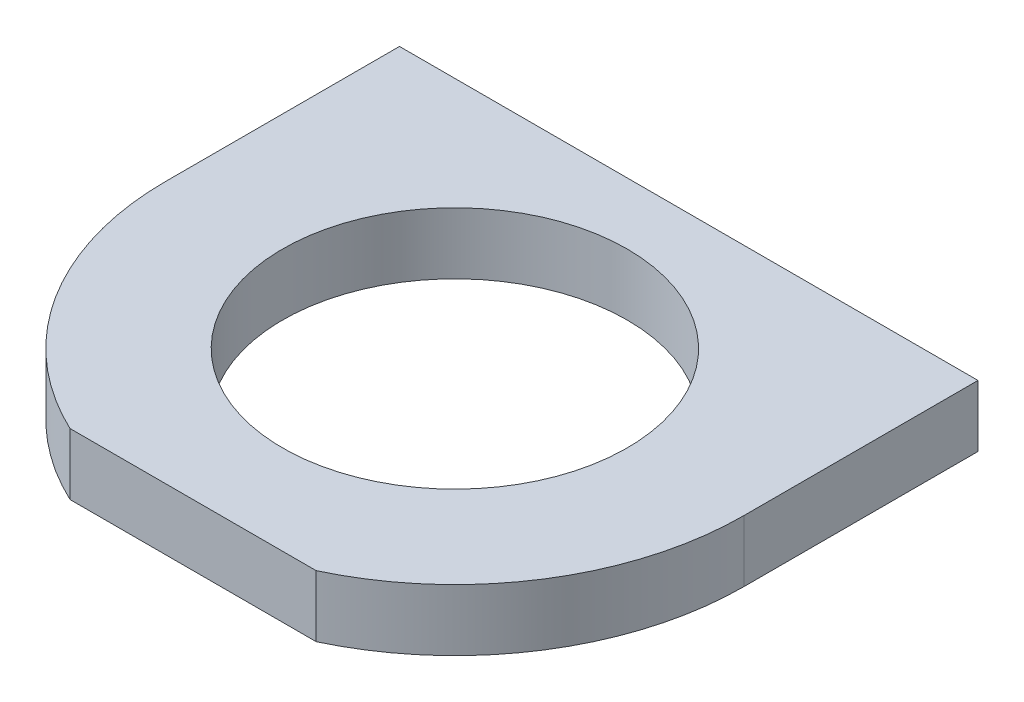
SolidWorks part; units mm, degrees
material "ｱｸﾘﾙ (中-上級の耐衝撃性)"
ref_plane "正面" through (0, 0, 0) normal (0, 0, 1) x (1, 0, 0)
ref_plane "平面" through (0, 0, 0) normal (0, 1, 0) x (1, 0, 0)
ref_plane "右側面" through (0, 0, 0) normal (1, 0, 0) x (0, 0, -1)
sketch "ｽｹｯﾁ1" plane through (0, 0, 0) normal (0, 0, 1) x (1, 0, 0)
  line L1 (-23.5, 2.5) -> (23.5, 2.5)
  line L2 (-23.5, 2.5) -> (-23.5, -2.5)
  line L3 (-23.5, -2.5) -> (23.5, -2.5)
  line L4 (23.5, 2.5) -> (23.5, -2.5)
  line L5 (-23.5, 2.5) -> (23.5, -2.5) construction
  line L6 (-23.5, -2.5) -> (23.5, 2.5) construction
  point P0 (0, 0)
  dimension "D1" = 5
  dimension "D2" = 47
extrude "ﾎﾞｽ - 押し出し1" add sketch "ｽｹｯﾁ1" along normal blind 19 contours L1 L4 L3 L2
sketch "ｽｹｯﾁ2" plane through (0, -2.5, 0) normal (0, -1, 0) x (1, 0, 0)
  line L0 (-23.5, 19) -> (23.5, 19) construction
  circle A0 centre (0, 19) radius 23.5
extrude "ﾎﾞｽ - 押し出し2" add sketch "ｽｹｯﾁ2" against normal blind 5
sketch "ｽｹｯﾁ3" plane through (0, -2.5, 0) normal (0, -1, 0) x (1, 0, 0)
  line L0 (-23.5, 19) -> (23.5, 19)
  line L1 (23.5, 19) -> (23.5, 0) construction
  line L2 (-23.5, 19) -> (-23.5, 0) construction
  line L3 (0, 19) -> (-14, 19)
  arc A0 (23.5, 19) -> (-23.5, 19) centre (0, 19) ccw construction
  circle A2 centre (0, 19) radius 14
  dimension "D3" = 28
sketch "ｽｹｯﾁ4" plane through (0, 0, 0) normal (0, 0, -1) x (-1, 0, 0)
  line L0 (0, 0) -> (-18, 0)
  line L1 (0, 0) -> (18, 0)
  dimension "D1" = 18
  dimension "D2" = 18
hole_wizard "M2.5x0.45 ねじ穴1" positions "ｽｹｯﾁ6" profile "ｽｹｯﾁ5" tap size "M2.5x0.45" standard "JIS"
sketch "ｽｹｯﾁ6" plane through (0, 0, 0) normal (0, 0, -1) x (-1, 0, 0)
  point P0 (18, 0)
  point P3 (-18, 0)
sketch "ｽｹｯﾁ5" plane through (-18, 0, 0) normal (1, 0, 0) x (0, 1, 0)
  line L0 (0, 0) -> (0, 7.8659)
  line L1 (0, 7.8659) -> (1.025, 7.25)
  line L2 (1.025, 7.25) -> (1.025, 0)
  line L5 (1.025, 0) -> (0, 0)
  line L10 (0, 7.8659) -> (-1.025, 7.25) construction
  line L11 (0, -6.35) -> (0, 107.95) construction
  dimension "ねじ下穴ﾄﾞﾘﾙ直径" = 2.05
  dimension "ねじ下穴ﾄﾞﾘﾙの深さ" = 7.25
  dimension "ﾄﾞﾘﾙ角度" = 118
cosmetic thread "穴のねじ山1" parameters "D1"=5, "D2"=2.5
cosmetic thread "穴のねじ山2" parameters "D1"=5, "D2"=2.5
ref_plane "平面1" through (23.5, -2.5, 0) normal (0, 0, -1) x (-1, 0, 0)
extrude "ｶｯﾄ - 押し出し1" cut sketch "ｽｹｯﾁ3" against normal blind 5 contours L0 A2 | L0 A2
sketch "ｽｹｯﾁ10" plane through (0, -2.5, 0) normal (0, -1, 0) x (1, 0, 0)
  line L0 (13.8293, 0) -> (-13.8293, 0)
extrude "ｶｯﾄ - 押し出し2" cut sketch "ｽｹｯﾁ10" against normal through all and the other way through all
sketch "ｽｹｯﾁ11" plane through (0, 2.5, 0) normal (0, 1, 0) x (1, 0, 0)
  line L0 (-10, -40.2662) -> (10, -40.2662)
  arc A0 (-23.5, -19) -> (23.5, -19) centre (0, -19) ccw construction
  arc A1 (-10, -40.2662) -> (10, -40.2662) centre (0, -19) ccw
  dimension "D1" = 20
extrude "ｶｯﾄ - 押し出し3" cut sketch "ｽｹｯﾁ11" against normal blind 5
